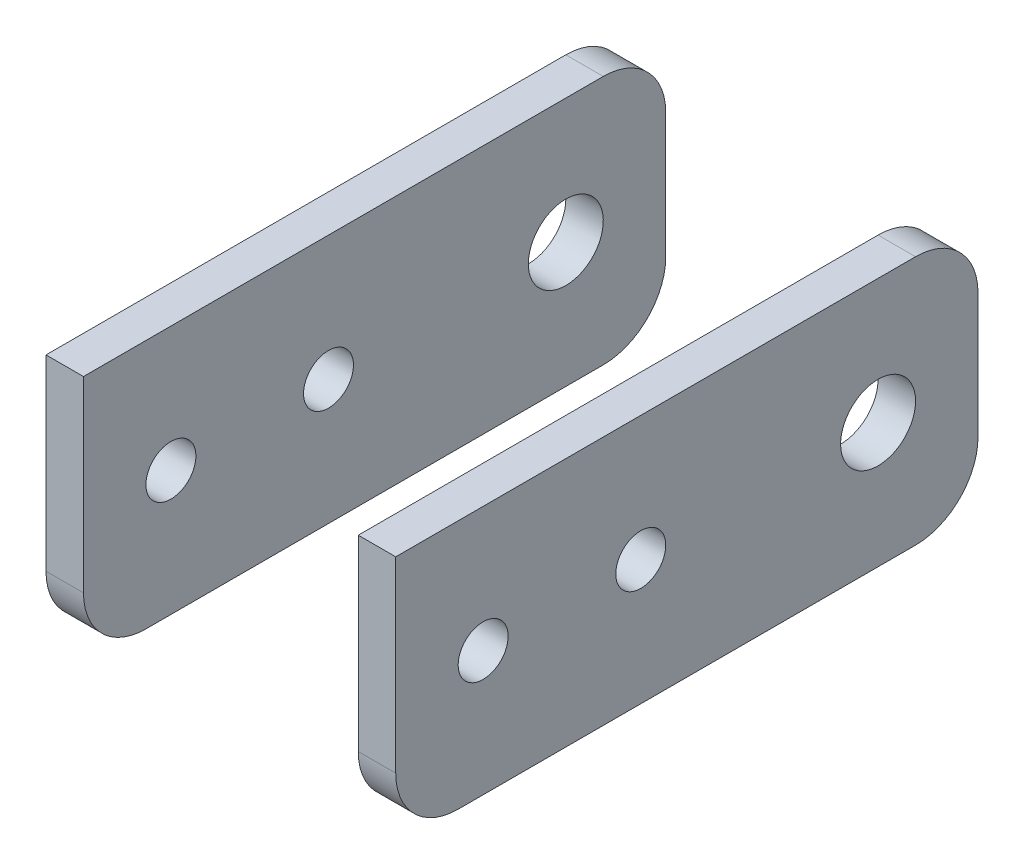
SolidWorks part; units mm, degrees
material "7075-T6 (SN)"
ref_plane "Płaszczyzna przednia" through (0, 0, 0) normal (0, 0, 1) x (1, 0, 0)
ref_plane "Płaszczyzna górna" through (0, 0, 0) normal (0, 1, 0) x (1, 0, 0)
ref_plane "Płaszczyzna prawa" through (0, 0, 0) normal (1, 0, 0) x (0, 0, -1)
sketch "Szkic1" plane through (0, 0, 0) normal (1, 0, 0) x (0, 0, -1)
  line L1 (0, 0) -> (-26.6169, 0)
  line L4 (-31.6169, 5) -> (-31.6169, 20)
  line L6 (7, 10) -> (-24.6169, 10) construction
  line L9 (0, 0) -> (10, 0)
  line L10 (15, 15) -> (15, 5)
  line L11 (10, 20) -> (5, 20)
  line L15 (5, 20) -> (-31.6169, 20)
  line L16 (0, 20) -> (0, -0.6012) construction
  circle A3 centre (-24.6169, 10) radius 2
  circle A5 centre (-12, 10) radius 2
  arc A6 (-31.6169, 5) -> (-26.6169, 0) centre (-26.6169, 5) ccw
  arc A7 (15, 5) -> (10, 0) centre (10, 5) cw
  circle A10 centre (7, 10) radius 3
  arc A14 (10, 20) -> (15, 15) centre (10, 15) cw
  point P7 (-14.5993, 75)
  point P25 (-31.6169, 0)
  point P28 (15, 0)
  point P33 (-31.6169, 50)
  point P34 (-6.7403, 71.608)
  point P41 (0, 20)
  dimension "D4" = 4
  dimension "D10" = 4
  dimension "D19" = 5
  dimension "D21" = 6
  dimension "D2" = 50
  dimension "D7" = 15
  dimension "D11" = 10
  dimension "D12" = 7
  dimension "D22" = 8
  dimension "D23" = 10
  dimension "D24" = 10
extrude "Dodanie-wyciągnięcie1" add sketch "Szkic1" along normal mid plane 28
sketch "Szkic2" plane through (0, 0, 0) normal (0, 0, 1) x (1, 0, 0)
  line L1 (-11, 20) -> (11, 20)
  line L2 (-11, 20) -> (-11, 0)
  line L3 (-11, 0) -> (11, 0)
  line L4 (11, 20) -> (11, 0)
  line L5 (14, 0) -> (-14, 0) construction
  line L6 (-14, 20) -> (-14, 5) construction
  line L7 (14, 20) -> (14, 5) construction
  line L8 (14, 20) -> (-14, 20) construction
  dimension "D1" = 3
  dimension "D2" = 3
extrude "Wytnij-wyciągnięcie1" cut sketch "Szkic2" against normal through all and the other way through all
